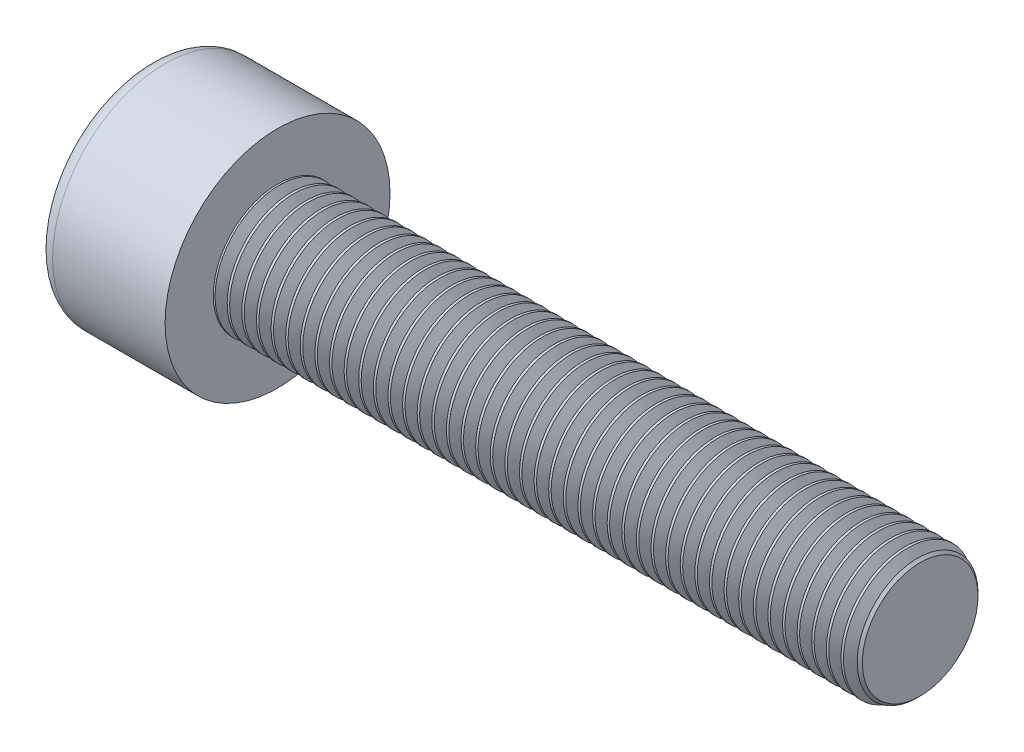
SolidWorks part; units mm, degrees
ref_plane "Front" through (0, 0, 0) normal (0, 0, 1) x (1, 0, 0)
ref_plane "Top" through (0, 0, 0) normal (0, 1, 0) x (1, 0, 0)
ref_plane "Right" through (0, 0, 0) normal (1, 0, 0) x (0, 0, -1)
sketch "Sketch1" plane through (0, 0, 0) normal (1, 0, 0) x (0, 0, -1)
  circle A0 centre (0, 0) radius 3.5
  dimension "dk" = 7
extrude "BaseHead" add sketch "Sketch1" along normal blind 4
sketch "Sketch2" plane through (4, 0, 0) normal (1, 0, 0) x (0, 0, -1)
  circle A0 centre (0, 0) radius 2
  dimension "d" = 4
extrude "BaseBody" add sketch "Sketch2" along normal blind 20
cosmetic thread "ThreadCosmetic1" [suppressed] parameters "b"=20, "D2"=3.242
sketch "Sketch3" plane through (0, 0, 0) normal (1, 0, 0) x (0, 0, -1)
  line L1 (1.7321, 0) -> (0.866, 1.5)
  line L2 (0.866, 1.5) -> (-0.866, 1.5)
  line L3 (-0.866, 1.5) -> (-1.7321, 0)
  line L4 (-1.7321, 0) -> (-0.866, -1.5)
  line L5 (-0.866, -1.5) -> (0.866, -1.5)
  line L6 (0.866, -1.5) -> (1.7321, 0)
  circle A0 centre (0, 0) radius 1.5 construction
  dimension "s" = 3
  dimension "e" = 3.4641
extrude "HexagonSocket" cut sketch "Sketch3" along normal blind 2
sketch "Sketch4" plane through (-4.1961, 0.75, 0) normal (0, 0, 1) x (-1, 0, 0)
  line L0 (-6.1961, 2.25) -> (-7.0622, 0.75)
  line L2 (-7.0622, 0.75) -> (-6.1961, 0.75)
  line L3 (-6.1961, 0.75) -> (-6.1961, 2.25)
  line L4 (-5.0351, 0.75) -> (0.839, 0.75) construction
  line L5 (-28.1961, 0.75) -> (-8.1961, 0.75) construction
  line L6 (-8.1961, 0.75) -> (-4.1961, 0.75) construction
  dimension "m" = 60
revolve "Cut-Revolve1" cut sketch "Sketch4" angle 360 about L4
fillet "HeadFillet" [suppressed] radius 0.2
fillet "TopFillet" radius 0.5 1 edges at (0, 0, -3.5)
chamfer "Chamfer1" distance 0.2 angle 45 1 edges at (24, 0, -2)
sketch "Sketch5" plane through (0, 0, 0) normal (0, 0, 1) x (1, 0, 0)
  line L0 (23.8, 1.6718) -> (23.9895, 2)
  line L1 (23.9895, 2) -> (23.9895, 2.379)
  line L2 (23.9895, 2.379) -> (23.6105, 2.379)
  line L3 (23.6105, 2.379) -> (23.6105, 2)
  line L4 (23.6105, 2) -> (23.8, 1.6718)
  line L5 (0, 0) -> (7.8886, 0) construction
  line L6 (23.8, -2) -> (23.8, 2) construction
  dimension "D1" = 4
  dimension "D2" = 0.379
revolve "Cut-Revolve10" cut sketch "Sketch5" angle 360 about L5
pattern_linear "LPattern10" count 44 spacing 0.4548 along (-1, 0, 0) of "Cut-Revolve10"
equation "\"r1@TopFillet\" = \"d@Sketch2\" / 8"
equation "\"D1@Chamfer1\" = \"r@HeadFillet\""
equation "\"D1@Sketch5\" = \"d@Sketch2\""
equation "\"D2@Sketch5\" =  ( \"d@Sketch2\" - \"D2@ThreadCosmetic1\" )  / 2"
equation "\"D3@LPattern10\" = \"D2@Sketch5\" * 1.2"
equation "\"D1@LPattern10\" = \"b@ThreadCosmetic1\" / \"D3@LPattern10\""
